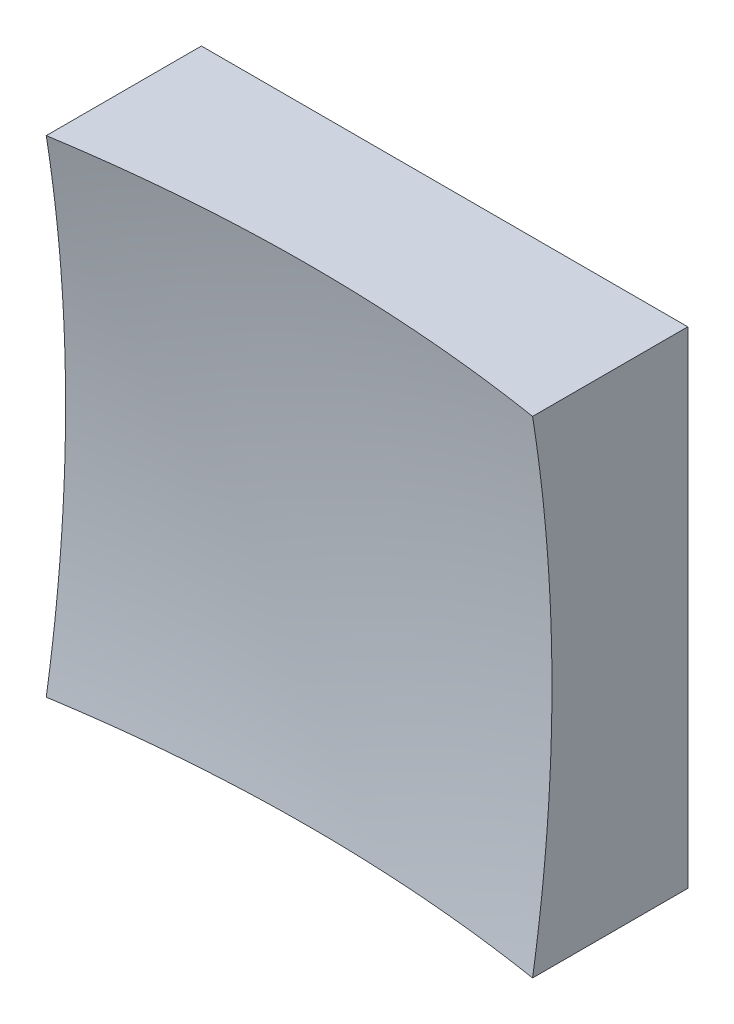
SolidWorks part; units mm, degrees
ref_plane "前视基准面" through (0, 0, 0) normal (0, 0, 1) x (1, 0, 0)
ref_plane "上视基准面" through (0, 0, 0) normal (0, 1, 0) x (1, 0, 0)
ref_plane "右视基准面" through (0, 0, 0) normal (1, 0, 0) x (0, 0, -1)
sketch "草图1" plane through (0, 0, 0) normal (0, 0, 1) x (1, 0, 0)
  line L1 (-12.5, 12.5) -> (12.5, 12.5)
  line L2 (-12.5, 12.5) -> (-12.5, -12.5)
  line L3 (-12.5, -12.5) -> (12.5, -12.5)
  line L4 (12.5, 12.5) -> (12.5, -12.5)
  line L5 (-12.5, 12.5) -> (12.5, -12.5) construction
  line L6 (-12.5, -12.5) -> (12.5, 12.5) construction
  point P0 (0, 0)
  dimension "D1" = 25
  dimension "D2" = 25
extrude "凸台-拉伸1" add sketch "草图1" along normal blind 20 contours L2 L3 L4 L1
sketch "草图2" plane through (0, 0, 0) normal (0, 1, 0) x (1, 0, 0)
  line L0 (-7.4603, -6) -> (7.3192, -6) construction
  line L1 (0, 0) -> (0, -12.1749) construction
  line L2 (77.9876, -68.1695) -> (0, -68.1695)
  line L3 (0, -68.1695) -> (0, -6)
  arc A1 (77.9876, -68.1695) -> (0, -6) centre (0, -86) ccw
  dimension "D2" = 160
  dimension "D1" = 6
revolve "切除-旋转2" cut sketch "草图2" angle 360 about L3
